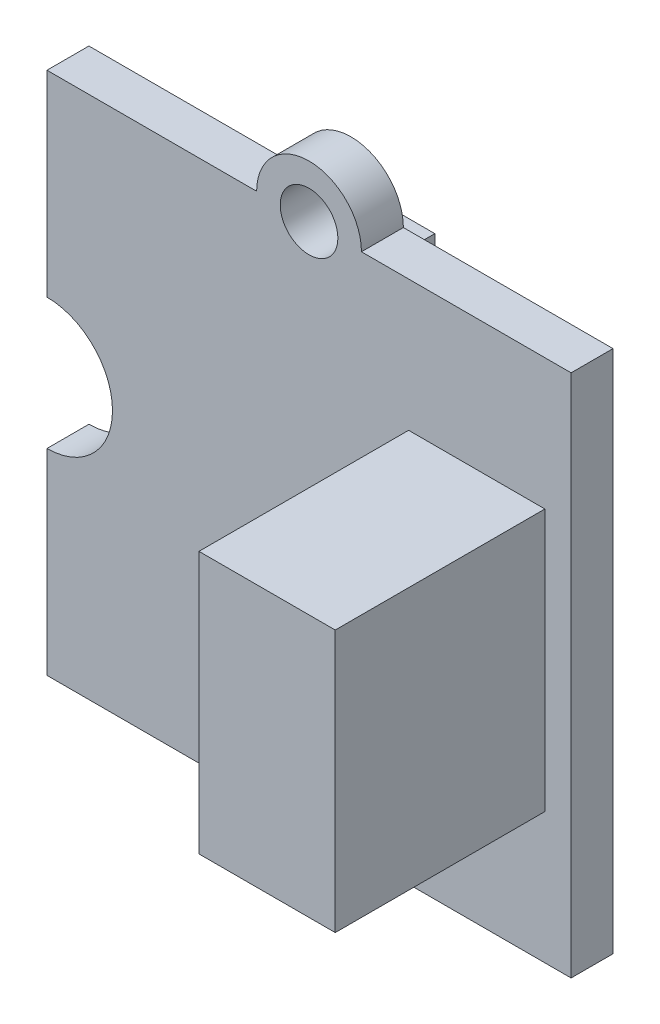
SolidWorks part; units mm, degrees
ref_plane "正面" through (0, 0, 0) normal (1, 0, 0) x (0, 1, 0)
ref_plane "平面" through (0, 0, 0) normal (0, 0, 1) x (0, 1, 0)
ref_plane "右側面" through (0, 0, 0) normal (0, 1, 0) x (-1, 0, 0)
sketch "ｽｹｯﾁ1" plane through (0, 0, 0) normal (0, 0, 1) x (0, 1, 0)
  line L1 (0, 0) -> (20, 0)
  line L2 (0, 0) -> (0, 20)
  line L3 (0, 20) -> (20, 20)
  line L4 (20, 0) -> (20, 20)
  line L5 (0, 0) -> (20, 20) construction
  line L6 (0, 20) -> (20, 0) construction
  circle A0 centre (0, 10) radius 2
  circle A1 centre (20, 10) radius 2
  circle A2 centre (0, 10) radius 1.1
  circle A3 centre (20, 10) radius 1.1
  circle A4 centre (10, 20) radius 2.5
  point P4 (10, 10)
  dimension "D3" = 4
  dimension "D4" = 2.2
  dimension "D5" = 5
  dimension "D1" = 20
  dimension "D2" = 20
extrude "ﾎﾞｽ - 押し出し1" add sketch "ｽｹｯﾁ1" along normal blind 1.6 contours A1 L4 L3 L2 A0 L1 | A3 L4 A1 | A3 L4 A1 | A2 L2 A0 | A2 L2 A0
sketch "ｽｹｯﾁ2" plane through (0, 0, 0) normal (0, 0, -1) x (1, 0, 0)
  line L0 (0, 0) -> (0, -20) construction
  line L1 (-12.8, -14.4) -> (-17.4, -14.4)
  line L2 (-12.8, -14.4) -> (-12.8, -5.6)
  line L3 (-12.8, -5.6) -> (-17.4, -5.6)
  line L4 (-17.4, -14.4) -> (-17.4, -5.6)
  line L5 (-12.8, -14.4) -> (-17.4, -5.6) construction
  line L6 (-12.8, -5.6) -> (-17.4, -14.4) construction
  line L7 (-20, 0) -> (-20, -7.5) construction
  point P0 (-15.1, -10)
  point P8 (0, 0)
  point P9 (0, 0)
  point P12 (0, -10)
  dimension "D1" = 4.6
  dimension "D2" = 8.8
  dimension "D3" = 2.6
extrude "ﾎﾞｽ - 押し出し2" add sketch "ｽｹｯﾁ2" along normal blind 6
sketch "ｽｹｯﾁ3" plane through (0, 0, 1.6) normal (0, 0, 1) x (1, 0, 0)
  line L0 (0, 0) -> (0, 20) construction
  line L1 (-1, 5) -> (-6.2, 5)
  line L2 (-1, 5) -> (-1, 15)
  line L3 (-1, 15) -> (-6.2, 15)
  line L4 (-6.2, 5) -> (-6.2, 15)
  line L5 (-1, 5) -> (-6.2, 15) construction
  line L6 (-1, 15) -> (-6.2, 5) construction
  point P0 (-3.6, 10)
  point P5 (0, 0)
  point P8 (0, 10)
  dimension "D1" = 10
  dimension "D2" = 5.2
  dimension "D3" = 1
extrude "ﾎﾞｽ - 押し出し3" add sketch "ｽｹｯﾁ3" along normal blind 8
